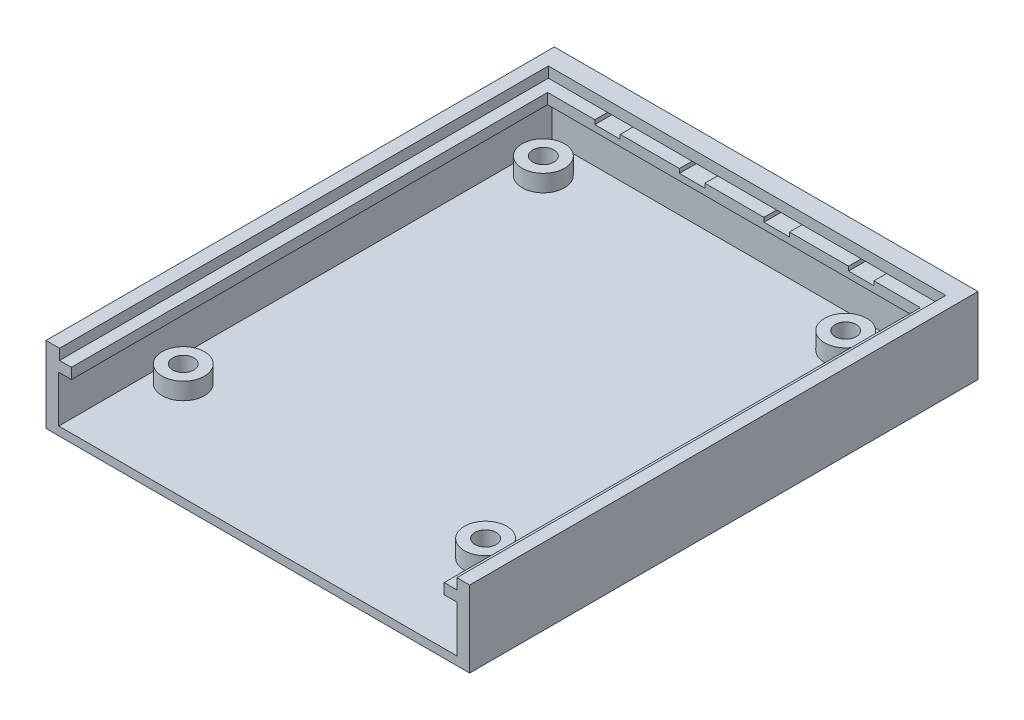
SolidWorks part; units mm, degrees
other "Uwaga1"
sketch "Szkic9" plane through (23.8372, 18, 80.1163) normal (0.0402, 0.0409, 0.9984) x (0.0516, -0.9979, 0.0388)
ref_plane "Płaszczyzna przednia" through (0, 0, 0) normal (0, 0, 1) x (1, 0, 0)
ref_plane "Płaszczyzna górna" through (0, 0, 0) normal (0, 1, 0) x (1, 0, 0)
ref_plane "Płaszczyzna prawa" through (0, 0, 0) normal (1, 0, 0) x (0, 0, -1)
sketch "Szkic1" plane through (0, 0, 0) normal (0, 1, 0) x (1, 0, 0)
  line L1 (-76.1628, 39.8837) -> (23.8372, 39.8837)
  line L2 (-76.1628, 39.8837) -> (-76.1628, -80.1163)
  line L3 (-76.1628, -80.1163) -> (23.8372, -80.1163)
  line L4 (23.8372, 39.8837) -> (23.8372, -80.1163)
  line L5 (-76.1628, 39.8837) -> (23.8372, -80.1163) construction
  line L6 (-76.1628, -80.1163) -> (23.8372, 39.8837) construction
  line L7 (-73.1628, -76.5163) -> (20.8372, -76.5163)
  line L8 (-73.1628, -76.5163) -> (-73.1628, 36.2837)
  line L9 (-73.1628, 36.2837) -> (20.8372, 36.2837)
  line L10 (20.8372, -76.5163) -> (20.8372, 36.2837)
  line L11 (-73.1628, -76.5163) -> (20.8372, 36.2837) construction
  line L12 (-73.1628, 36.2837) -> (20.8372, -76.5163) construction
  circle A0 centre (-67.1628, 28.2837) radius 2.5
  circle A1 centre (-67.1628, 28.2837) radius 5
  circle A2 centre (4.2072, 28.2837) radius 2.5
  circle A3 centre (4.2072, 28.2837) radius 5
  circle A4 centre (4.2072, -56.7163) radius 2.5
  circle A5 centre (4.2072, -56.7163) radius 5
  circle A6 centre (-67.1628, -56.7163) radius 2.5
  circle A7 centre (-67.1628, -56.7163) radius 5
  point P0 (-26.1628, -20.1163)
  point P7 (-26.1628, -20.1163)
  dimension "D4" = 5
  dimension "D5" = 10
  dimension "D9" = 8
  dimension "D1" = 100
  dimension "D2" = 120
  dimension "D3" = 3
  dimension "D8" = 6
  dimension "D10" = 71.37
  dimension "D11" = 85
  dimension "D6" = 2
  dimension "D7" = 2
ref_plane "Płaszczyzna1" through (0, 13.7007, 77.7005) normal (0, 0.1736, 0.9848) x (1, 0, 0)
extrude "Dodanie-wyciągnięcie3" add sketch "Szkic1" along normal blind 2 contours L2 L3 L4 L1
sketch "Szkic3" plane through (0, 2, 0) normal (0, 1, 0) x (1, 0, 0)
  circle A0 centre (-67.1628, 28.2837) radius 5
  circle A1 centre (-67.1628, 28.2837) radius 2.5
  circle A2 centre (4.2072, 28.2837) radius 2.5
  circle A3 centre (4.2072, 28.2837) radius 5
  circle A4 centre (4.2072, -56.7163) radius 2.5
  circle A5 centre (4.2072, -56.7163) radius 5
  circle A6 centre (-67.1628, -56.7163) radius 2.5
  circle A7 centre (-67.1628, -56.7163) radius 5
  dimension "D3" = 5
  dimension "D4" = 10
  dimension "D6" = 71.37
  dimension "D5" = 85
  dimension "D1" = 2
  dimension "D2" = 2
extrude "Dodanie-wyciągnięcie4" add sketch "Szkic3" along normal blind 4
sketch "Szkic4" plane through (0, 2, 0) normal (0, 1, 0) x (1, 0, 0)
  line L0 (20.8372, -76.5163) -> (20.8372, 36.2837) construction
  line L1 (-76.1628, -80.1163) -> (23.8372, -80.1163)
  line L2 (-76.1628, -80.1163) -> (-76.1628, 39.8837)
  line L3 (-76.1628, 39.8837) -> (23.8372, 39.8837)
  line L4 (23.8372, -80.1163) -> (23.8372, 39.8837)
  line L5 (-76.1628, -80.1163) -> (23.8372, 39.8837) construction
  line L6 (-76.1628, 39.8837) -> (23.8372, -80.1163) construction
  line L7 (-73.1628, -76.5163) -> (20.8372, -76.5163)
  line L8 (-73.1628, -76.5163) -> (-73.1628, 36.2837)
  line L9 (-73.1628, 36.2837) -> (20.8372, 36.2837)
  line L10 (20.8372, -76.5163) -> (20.8372, 36.2837)
  line L11 (-73.1628, -76.5163) -> (20.8372, 36.2837) construction
  line L12 (-73.1628, 36.2837) -> (20.8372, -76.5163) construction
  line L13 (20.8372, -76.5163) -> (20.8372, -80.1163)
  line L14 (-73.1628, -76.5163) -> (-73.1628, -80.1163)
  point P0 (-26.1628, -20.1163)
  point P6 (-26.1628, -20.1163)
  circle M9 centre (-67.1628, -56.7163) radius 5
  circle M10 centre (4.2072, -56.7163) radius 5
  circle M11 centre (4.2072, 28.2837) radius 5
  circle M12 centre (-67.1628, 28.2837) radius 5
extrude "Dodanie-wyciągnięcie5" add sketch "Szkic4" along normal blind 16 contours L7 L14 L1 L13 | L7 L10 L9 L8 M9 M11 M12 M10
sketch "Szkic6" plane through (0, 0, -36.2837) normal (0, 0, 1) x (1, 0, 0)
  line L0 (20.8372, 18) -> (20.8372, 2) construction
  line L1 (-73.1628, 18) -> (20.8372, 18)
  line L2 (-73.1628, 18) -> (-73.1628, 13)
  line L3 (-73.1628, 13) -> (20.8372, 13)
  line L4 (20.8372, 18) -> (20.8372, 13)
  dimension "D1" = 5
extrude "Dodanie-wyciągnięcie6" add sketch "Szkic6" along normal blind 4
sketch "Szkic7" plane through (20.8372, 0, 0) normal (-1, 0, 0) x (0, 0, 1)
  line L1 (80.1163, 18) -> (-32.2837, 18)
  line L2 (80.1163, 18) -> (80.1163, 13)
  line L3 (80.1163, 13) -> (-32.2837, 13)
  line L4 (-32.2837, 18) -> (-32.2837, 13)
sketch "Szkic8" plane through (-73.1628, 0, 0) normal (1, 0, 0) x (0, 0, -1)
  line L1 (-80.1163, 18) -> (32.2837, 18)
  line L2 (-80.1163, 18) -> (-80.1163, 13)
  line L3 (-80.1163, 13) -> (32.2837, 13)
  line L4 (32.2837, 18) -> (32.2837, 13)
extrude "Dodanie-wyciągnięcie7" add sketch "Szkic7" along normal blind 3
extrude "Dodanie-wyciągnięcie8" add sketch "Szkic8" along normal blind 3
sketch "Szkic10" plane through (0, 18, 0) normal (0, 1, 0) x (1, 0, 0)
  line L0 (-70.1628, -80.1163) -> (-72.9727, -80.1163)
  line L1 (-72.9727, -80.1163) -> (-72.9727, 35.2837)
  line L2 (-72.9727, 35.2837) -> (20.8372, 35.2837)
  line L3 (20.8372, 35.2837) -> (20.8372, -80.1163)
  line L4 (17.8372, -80.1163) -> (23.8372, -80.1163) construction
  line L5 (20.8372, -80.1163) -> (17.8372, -80.1163)
  line L6 (17.8372, -80.1163) -> (17.8372, 32.2837)
  line L7 (17.8372, 32.2837) -> (-70.1628, 32.2837)
  line L8 (-70.1628, 32.2837) -> (-70.1628, -80.1163)
  dimension "D1" = 2.8099
  dimension "D2" = 3
extrude "Wytnij-wyciągnięcie1" cut sketch "Szkic10" against normal blind 2.5
sketch "Szkic11" plane through (0, 15.5, 0) normal (0, 1, 0) x (1, 0, 0)
  line L0 (-59.0107, 32.2837) -> (-72.9727, 32.2837)
  line L1 (-59.0107, 32.2837) -> (-53.0107, 32.2837)
  line L2 (-59.0107, 32.2837) -> (-59.0107, 37.8837)
  line L3 (-59.0107, 37.8837) -> (-53.0107, 37.8837)
  line L4 (-53.0107, 32.2837) -> (-53.0107, 37.8837)
  line L5 (-39.0487, 32.2837) -> (-53.0107, 32.2837)
  line L6 (-39.0487, 32.2837) -> (-33.0487, 32.2837)
  line L7 (-39.0487, 32.2837) -> (-39.0487, 37.8837)
  line L8 (-39.0487, 37.8837) -> (-33.0487, 37.8837)
  line L9 (-33.0487, 32.2837) -> (-33.0487, 37.8837)
  line L10 (-19.0868, 32.2837) -> (-33.0487, 32.2837)
  line L11 (-19.0868, 32.2837) -> (-13.0868, 32.2837)
  line L12 (-19.0868, 32.2837) -> (-19.0868, 37.8837)
  line L13 (-19.0868, 37.8837) -> (-13.0868, 37.8837)
  line L14 (-13.0868, 32.2837) -> (-13.0868, 37.8837)
  line L15 (0.8752, 32.2837) -> (-13.0868, 32.2837)
  line L16 (0.8752, 32.2837) -> (6.8752, 32.2837)
  line L17 (0.8752, 32.2837) -> (0.8752, 37.8837)
  line L18 (0.8752, 37.8837) -> (6.8752, 37.8837)
  line L19 (6.8752, 32.2837) -> (6.8752, 37.8837)
  line L20 (-72.9727, 35.2837) -> (-72.9727, -80.1163) construction
  line L21 (6.8752, 32.2837) -> (20.8372, 32.2837)
  line L24 (20.8372, -80.1163) -> (20.8372, 35.2837) construction
  line L25 (-76.1628, 39.8837) -> (23.8372, 39.8837) construction
  line L26 (-70.1628, 32.2837) -> (17.8372, 32.2837) construction
  line M23 (-70.1628, 32.2837) -> (17.8372, 32.2837)
  line M27 (20.8372, 35.2837) -> (-72.9727, 35.2837)
  dimension "D2" = 6
  dimension "D3" = 2
  dimension "D1" = 4
extrude "Wytnij-wyciągnięcie3" cut sketch "Szkic11" against normal blind 1 contours L4 L2 M23 M27 | L4 L3 L2 M27 | L9 L7 M23 M27 | L9 L8 L7 M27 | L14 L12 M23 M27 | L14 L13 L12 M27 | L19 L17 M23 M27 | L19 L18 L17 M27
